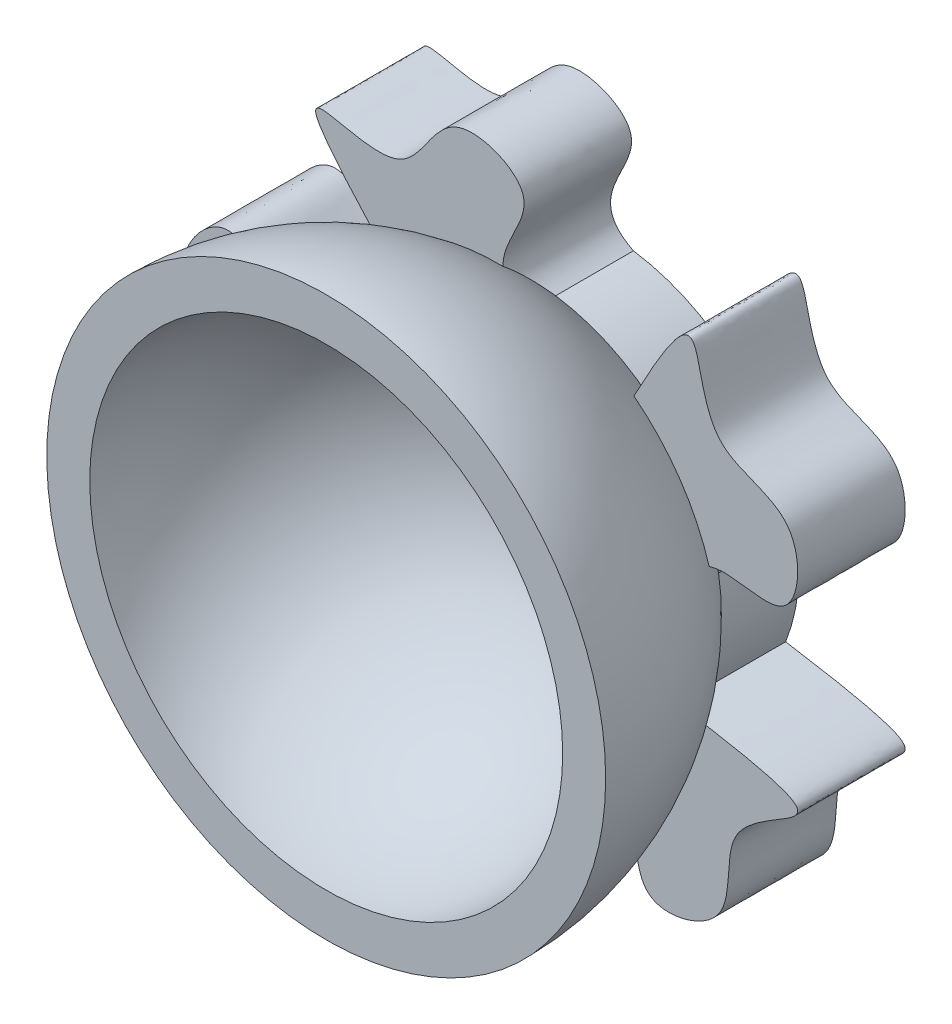
SolidWorks part; units mm, degrees
ref_plane "Front Plane" through (0, 0, 0) normal (0, 0, 1) x (1, 0, 0)
ref_plane "Top Plane" through (0, 0, 0) normal (0, 1, 0) x (1, 0, 0)
ref_plane "Right Plane" through (0, 0, 0) normal (1, 0, 0) x (0, 0, -1)
sketch "Sketch1" plane through (0, 0, 0) normal (0, 0, 1) x (1, 0, 0)
  line L0 (0, 21.5) -> (0, -21.5)
  arc A0 (0, -21.5) -> (0, 21.5) centre (0, 0) ccw
  dimension "D1" = 43
ref_plane "Plane1" through (0, 0, 21.5) normal (0, 0, 1) x (1, 0, 0)
sketch "Sketch2" plane through (0, 0, 21.5) normal (0, 0, 1) x (1, 0, 0)
  circle A0 centre (0, 0) radius 10.75
  dimension "D1" = 21.5
sketch "Sketch3" plane through (0, 0, 21.5) normal (0, 0, 1) x (1, 0, 0)
  circle A0 centre (0, 0) radius 10.75
  circle A1 centre (0, 0) radius 14.75
  dimension "D1" = 4
sketch "Sketch6" plane through (0, 0, 0) normal (0, 1, 0) x (1, 0, 0)
  line L2 (-22, 0) -> (-26, 0)
  line L3 (0, 22) -> (0, 26)
  line L4 (0, 0) -> (0, 22) construction
  line L5 (0, 26) -> (-18, 26)
  line L6 (-18, 26) -> (-18, 18.7617)
  arc A0 (0, 22) -> (-22, 0) centre (0, 0) ccw
  arc A1 (-18, 18.7617) -> (-26, 0) centre (0, 0) ccw
  dimension "D2" = 4
  dimension "D1" = 22
  dimension "D3" = 18
revolve "Revolve2" add sketch "Sketch6" angle 360 about L4
ref_plane "Plane2" through (0, 0, -26.5) normal (0, 0, 1) x (1, 0, 0)
sketch "Sketch8" plane through (0, 0, -26.5) normal (0, 0, 1) x (1, 0, 0)
sketch "Sketch9" plane through (0, 0, -26) normal (0, 0, -1) x (-1, 0, 0)
  circle A0 centre (0, 0) radius 18 construction
  circle A1 centre (0, 0) radius 26 construction
  arc A2 (17.4291, -4.4974) -> (16.1435, 7.9617) centre (0, 0) ccw
  circle A3 centre (0, 0) radius 18
  arc A4 (9.6632, 15.1863) -> (-2.5834, 17.8136) centre (0, 0) ccw
  arc A5 (1.1086, -17.9658) -> (12.5606, -12.893) centre (0, 0) ccw
  arc A6 (-16.7439, -6.6061) -> (-8.3806, -15.93) centre (0, 0) ccw
  arc A7 (-11.4569, 13.883) -> (-17.7401, 3.0477) centre (0, 0) ccw
  spline S0 degree 3 poles (-2.5834, 17.8136) (2.4774, 20.4093) (-6.8261, 26.9418) (5.3721, 31.8277) (8.686, 18.1038) (24.0133, 30.5865) (9.6632, 15.1863) knots 0 0 0 0 0.249532 0.40923 0.599395 1 1 1 1
  spline S1 degree 3 poles (16.1435, 7.9617) (20.1481, 3.9582) (23.5849, 14.7982) (31.7171, 4.8442) (21.24, -2.8346) (35.2215, -13.5105) (17.4291, -4.4974) knots 0 0 0 0 0.251711 0.412803 0.599959 1 1 1 1
  spline S2 degree 3 poles (12.5606, -12.893) (9.9906, -17.9388) (21.3621, -17.8577) (14.4082, -28.6678) (3.8677, -21.0763) (-1.9652, -37.6726) (1.1086, -17.9658) knots 0 0 0 0 0.251711 0.412803 0.599959 1 1 1 1
  spline S3 degree 3 poles (-8.3806, -15.93) (-13.9736, -15.045) (-10.3825, -25.8349) (-22.8123, -22.5618) (-18.8496, -10.1913) (-36.4361, -9.7725) (-16.7439, -6.6061) knots 0 0 0 0 0.251711 0.412803 0.599959 1 1 1 1
  spline S4 degree 3 poles (-17.7401, 3.0477) (-18.6267, 8.6405) (-27.7788, 1.8909) (-28.507, 14.7238) (-15.5174, 14.7778) (-20.5536, 31.6329) (-11.4569, 13.883) knots 0 0 0 0 0.251711 0.412803 0.599959 1 1 1 1
  dimension "D1" = 0
  dimension "D2" = 5
extrude "Boss-Extrude3" add sketch "Sketch9" against normal blind 10
